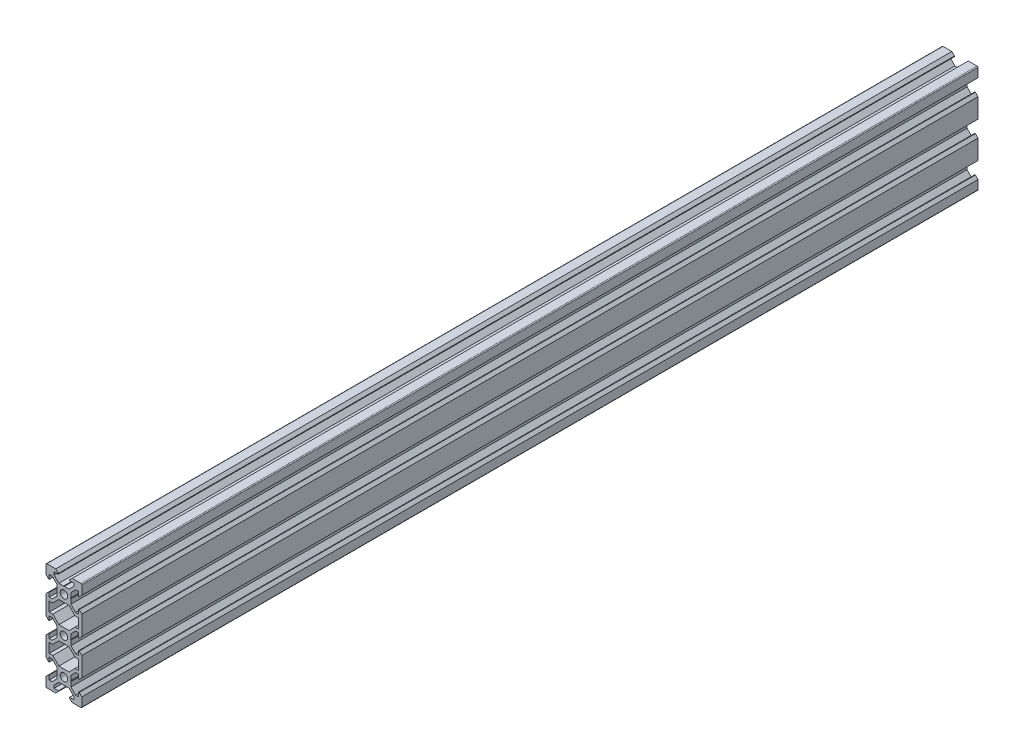
SolidWorks part; units mm, degrees
material "6061-T6 (SS)"
ref_plane "Front Plane" through (0, 0, 0) normal (0, 0, 1) x (1, 0, 0)
ref_plane "Top Plane" through (0, 0, 0) normal (0, 1, 0) x (1, 0, 0)
ref_plane "Right Plane" through (0, 0, 0) normal (1, 0, 0) x (0, 0, -1)
sketch "Sketch1" plane through (0, 0, 0) normal (0, 0, 1) x (1, 0, 0)
  line L0 (0, 0) -> (10, 0) construction
  line L1 (9.5, -30) -> (-9.5, -30)
  line L2 (10, -29.5) -> (10, 29.5)
  line L3 (9.5, 30) -> (-9.5, 30)
  line L4 (-10, -29.5) -> (-10, 29.5)
  line L5 (10, -30) -> (-10, 30) construction
  line L6 (10, 30) -> (-10, -30) construction
  circle A0 centre (0, 20) radius 2.1
  circle A1 centre (0, 0) radius 2.1
  circle A2 centre (0, -20) radius 2.1
  arc A3 (-9.5, -30) -> (-10, -29.5) centre (-9.5, -29.5) cw
  arc A4 (9.5, -30) -> (10, -29.5) centre (9.5, -29.5) ccw
  arc A5 (10, 29.5) -> (9.5, 30) centre (9.5, 29.5) ccw
  arc A6 (-9.5, 30) -> (-10, 29.5) centre (-9.5, 29.5) ccw
  point P0 (0, 0)
  line B0 (0, 20) -> (0, 30) construction
  line B1 (0, 23.69) -> (-0.21, 23.9)
  line B2 (-0.21, 23.9) -> (-2.8393, 23.9)
  line B3 (-2.8393, 23.9) -> (-5.5, 26.5607)
  line B4 (-5.5, 26.5607) -> (-5.5, 28.2)
  line B5 (-5.5, 28.2) -> (-3.125, 28.2)
  line B6 (-3.125, 28.2) -> (-3.125, 28.545)
  line B7 (-3.125, 28.545) -> (-4.58, 30)
  line B8 (-4.58, 30) -> (4.58, 30)
  line B9 (0, 20) -> (-5.9132, 25.9132) construction
  line B10 (3.125, 28.545) -> (4.58, 30)
  line B11 (3.125, 28.2) -> (3.125, 28.545)
  line B12 (5.5, 28.2) -> (3.125, 28.2)
  line B13 (5.5, 26.5607) -> (5.5, 28.2)
  line B14 (2.8393, 23.9) -> (5.5, 26.5607)
  line B15 (0.21, 23.9) -> (2.8393, 23.9)
  line B16 (0, 23.69) -> (0.21, 23.9)
  line B17 (0, 20) -> (-10, 20) construction
  line B18 (-3.69, 20) -> (-3.9, 19.79)
  line B19 (-3.9, 19.79) -> (-3.9, 17.1607)
  line B20 (-3.9, 17.1607) -> (-6.5607, 14.5)
  line B21 (-6.5607, 14.5) -> (-8.2, 14.5)
  line B22 (-8.2, 14.5) -> (-8.2, 16.875)
  line B23 (-8.2, 16.875) -> (-8.545, 16.875)
  line B24 (-8.545, 16.875) -> (-10, 15.42)
  line B25 (-10, 15.42) -> (-10, 24.58)
  line B26 (0, 20) -> (-5.9132, 14.0868) construction
  line B27 (-8.545, 23.125) -> (-10, 24.58)
  line B28 (-8.2, 23.125) -> (-8.545, 23.125)
  line B29 (-8.2, 25.5) -> (-8.2, 23.125)
  line B30 (-6.5607, 25.5) -> (-8.2, 25.5)
  line B31 (-3.9, 22.8393) -> (-6.5607, 25.5)
  line B32 (-3.9, 20.21) -> (-3.9, 22.8393)
  line B33 (-3.69, 20) -> (-3.9, 20.21)
  line B34 (0, 0) -> (-10, 0) construction
  line B35 (-3.69, 0) -> (-3.9, -0.21)
  line B36 (-3.9, -0.21) -> (-3.9, -2.8393)
  line B37 (-3.9, -2.8393) -> (-6.5607, -5.5)
  line B38 (-6.5607, -5.5) -> (-8.2, -5.5)
  line B39 (-8.2, -5.5) -> (-8.2, -3.125)
  line B40 (-8.2, -3.125) -> (-8.545, -3.125)
  line B41 (-8.545, -3.125) -> (-10, -4.58)
  line B42 (-10, -4.58) -> (-10, 4.58)
  line B43 (0, 0) -> (-5.9132, -5.9132) construction
  line B44 (-8.545, 3.125) -> (-10, 4.58)
  line B45 (-8.2, 3.125) -> (-8.545, 3.125)
  line B46 (-8.2, 5.5) -> (-8.2, 3.125)
  line B47 (-6.5607, 5.5) -> (-8.2, 5.5)
  line B48 (-3.9, 2.8393) -> (-6.5607, 5.5)
  line B49 (-3.9, 0.21) -> (-3.9, 2.8393)
  line B50 (-3.69, 0) -> (-3.9, 0.21)
  line B51 (0, -20) -> (-10, -20) construction
  line B52 (-3.69, -20) -> (-3.9, -20.21)
  line B53 (-3.9, -20.21) -> (-3.9, -22.8393)
  line B54 (-3.9, -22.8393) -> (-6.5607, -25.5)
  line B55 (-6.5607, -25.5) -> (-8.2, -25.5)
  line B56 (-8.2, -25.5) -> (-8.2, -23.125)
  line B57 (-8.2, -23.125) -> (-8.545, -23.125)
  line B58 (-8.545, -23.125) -> (-10, -24.58)
  line B59 (-10, -24.58) -> (-10, -15.42)
  line B60 (0, -20) -> (-5.9132, -25.9132) construction
  line B61 (-8.545, -16.875) -> (-10, -15.42)
  line B62 (-8.2, -16.875) -> (-8.545, -16.875)
  line B63 (-8.2, -14.5) -> (-8.2, -16.875)
  line B64 (-6.5607, -14.5) -> (-8.2, -14.5)
  line B65 (-3.9, -17.1607) -> (-6.5607, -14.5)
  line B66 (-3.9, -19.79) -> (-3.9, -17.1607)
  line B67 (-3.69, -20) -> (-3.9, -19.79)
  line B68 (0, -20) -> (0, -30) construction
  line B69 (0, -23.69) -> (0.21, -23.9)
  line B70 (0.21, -23.9) -> (2.8393, -23.9)
  line B71 (2.8393, -23.9) -> (5.5, -26.5607)
  line B72 (5.5, -26.5607) -> (5.5, -28.2)
  line B73 (5.5, -28.2) -> (3.125, -28.2)
  line B74 (3.125, -28.2) -> (3.125, -28.545)
  line B75 (3.125, -28.545) -> (4.58, -30)
  line B76 (4.58, -30) -> (-4.58, -30)
  line B77 (0, -20) -> (5.9132, -25.9132) construction
  line B78 (-3.125, -28.545) -> (-4.58, -30)
  line B79 (-3.125, -28.2) -> (-3.125, -28.545)
  line B80 (-5.5, -28.2) -> (-3.125, -28.2)
  line B81 (-5.5, -26.5607) -> (-5.5, -28.2)
  line B82 (-2.8393, -23.9) -> (-5.5, -26.5607)
  line B83 (-0.21, -23.9) -> (-2.8393, -23.9)
  line B84 (0, -23.69) -> (-0.21, -23.9)
  line B85 (0, -20) -> (10, -20) construction
  line B86 (3.69, -20) -> (3.9, -19.79)
  line B87 (3.9, -19.79) -> (3.9, -17.1607)
  line B88 (3.9, -17.1607) -> (6.5607, -14.5)
  line B89 (6.5607, -14.5) -> (8.2, -14.5)
  line B90 (8.2, -14.5) -> (8.2, -16.875)
  line B91 (8.2, -16.875) -> (8.545, -16.875)
  line B92 (8.545, -16.875) -> (10, -15.42)
  line B93 (10, -15.42) -> (10, -24.58)
  line B94 (0, -20) -> (5.9132, -14.0868) construction
  line B95 (8.545, -23.125) -> (10, -24.58)
  line B96 (8.2, -23.125) -> (8.545, -23.125)
  line B97 (8.2, -25.5) -> (8.2, -23.125)
  line B98 (6.5607, -25.5) -> (8.2, -25.5)
  line B99 (3.9, -22.8393) -> (6.5607, -25.5)
  line B100 (3.9, -20.21) -> (3.9, -22.8393)
  line B101 (3.69, -20) -> (3.9, -20.21)
  line B102 (0, 0) -> (10, 0) construction
  line B103 (3.69, 0) -> (3.9, 0.21)
  line B104 (3.9, 0.21) -> (3.9, 2.8393)
  line B105 (3.9, 2.8393) -> (6.5607, 5.5)
  line B106 (6.5607, 5.5) -> (8.2, 5.5)
  line B107 (8.2, 5.5) -> (8.2, 3.125)
  line B108 (8.2, 3.125) -> (8.545, 3.125)
  line B109 (8.545, 3.125) -> (10, 4.58)
  line B110 (10, 4.58) -> (10, -4.58)
  line B111 (0, 0) -> (5.9132, 5.9132) construction
  line B112 (8.545, -3.125) -> (10, -4.58)
  line B113 (8.2, -3.125) -> (8.545, -3.125)
  line B114 (8.2, -5.5) -> (8.2, -3.125)
  line B115 (6.5607, -5.5) -> (8.2, -5.5)
  line B116 (3.9, -2.8393) -> (6.5607, -5.5)
  line B117 (3.9, -0.21) -> (3.9, -2.8393)
  line B118 (3.69, 0) -> (3.9, -0.21)
  line B119 (0, 20) -> (10, 20) construction
  line B120 (3.69, 20) -> (3.9, 20.21)
  line B121 (3.9, 20.21) -> (3.9, 22.8393)
  line B122 (3.9, 22.8393) -> (6.5607, 25.5)
  line B123 (6.5607, 25.5) -> (8.2, 25.5)
  line B124 (8.2, 25.5) -> (8.2, 23.125)
  line B125 (8.2, 23.125) -> (8.545, 23.125)
  line B126 (8.545, 23.125) -> (10, 24.58)
  line B127 (10, 24.58) -> (10, 15.42)
  line B128 (0, 20) -> (5.9132, 25.9132) construction
  line B129 (8.545, 16.875) -> (10, 15.42)
  line B130 (8.2, 16.875) -> (8.545, 16.875)
  line B131 (8.2, 14.5) -> (8.2, 16.875)
  line B132 (6.5607, 14.5) -> (8.2, 14.5)
  line B133 (3.9, 17.1607) -> (6.5607, 14.5)
  line B134 (3.9, 19.79) -> (3.9, 17.1607)
  line B135 (3.69, 20) -> (3.9, 19.79)
  line B136 (-8.2, 7.3) -> (-8.2, 12.7)
  line B137 (-8.2, 12.7) -> (-6.2393, 12.7)
  line B138 (-6.2393, 12.7) -> (-2.8393, 16.1)
  line B139 (-2.8393, 16.1) -> (2.8393, 16.1)
  line B140 (0, 16.1) -> (0, 10) construction
  line B141 (0, 10) -> (-8.2, 10) construction
  line B142 (6.2393, 12.7) -> (2.8393, 16.1)
  line B143 (8.2, 12.7) -> (6.2393, 12.7)
  line B144 (8.2, 7.3) -> (8.2, 12.7)
  line B145 (8.2, 7.3) -> (6.2393, 7.3)
  line B146 (6.2393, 7.3) -> (2.8393, 3.9)
  line B147 (-2.8393, 3.9) -> (2.8393, 3.9)
  line B148 (-6.2393, 7.3) -> (-2.8393, 3.9)
  line B149 (-8.2, 7.3) -> (-6.2393, 7.3)
  line B150 (0, 16.1) -> (0, 20) construction
  line B151 (0, 20) -> (-5.0927, 14.9073) construction
  line B152 (-8.2, -12.7) -> (-8.2, -7.3)
  line B153 (-8.2, -7.3) -> (-6.2393, -7.3)
  line B154 (-6.2393, -7.3) -> (-2.8393, -3.9)
  line B155 (-2.8393, -3.9) -> (2.8393, -3.9)
  line B156 (0, -3.9) -> (0, -10) construction
  line B157 (0, -10) -> (-8.2, -10) construction
  line B158 (6.2393, -7.3) -> (2.8393, -3.9)
  line B159 (8.2, -7.3) -> (6.2393, -7.3)
  line B160 (8.2, -12.7) -> (8.2, -7.3)
  line B161 (8.2, -12.7) -> (6.2393, -12.7)
  line B162 (6.2393, -12.7) -> (2.8393, -16.1)
  line B163 (-2.8393, -16.1) -> (2.8393, -16.1)
  line B164 (-6.2393, -12.7) -> (-2.8393, -16.1)
  line B165 (-8.2, -12.7) -> (-6.2393, -12.7)
  line B166 (0, -3.9) -> (0, 0) construction
  line B167 (0, 0) -> (-5.0927, -5.0927) construction
  dimension "D3" = 4.2
  dimension "D5" = 0.5
  dimension "D1" = 20
  dimension "D2" = 60
  dimension "D4" = 40
sketch_block_instance "V Slot 1-4"
sketch_block "V Slot 1" parameters "D1"=10, "D2"=11, "D3"=4.3, "D4"=1.8, "D5"=0.21, "D6"=45, "D7"=9.16, "D8"=1.5, "D9"=6.25
sketch_block_instance "V Slot 1-5"
sketch_block_instance "V Slot 1-6"
sketch_block_instance "V Slot 1-7"
sketch_block_instance "V Slot 1-8"
sketch_block_instance "V Slot 1-9"
sketch_block_instance "V Slot 1-10"
sketch_block_instance "V Slot 1-11"
sketch_block_instance "Center Cutout 1-1"
sketch_block "Center Cutout 1" parameters "D1"=5.4, "D2"=12.2, "D3"=8.2, "D4"=45, "D5"=10, "D6"=1.5
sketch_block_instance "Center Cutout 1-2"
extrude "Boss-Extrude1" add sketch "Sketch1" along normal blind 500 contours B135 B120 B121 B122 B123 B124 B125 B126 L2 A5 L3 B10 B11 B12 B13 B14 B15 B16 B1 B2 B3 B4 B5 B6 B7 A6 L4 B27 B28 B29 B30 B31 B32 B33 B18 B19 B20 B21 B22 B23 B24 B44 B45 B46 B47 B48 B49 B50 B35
